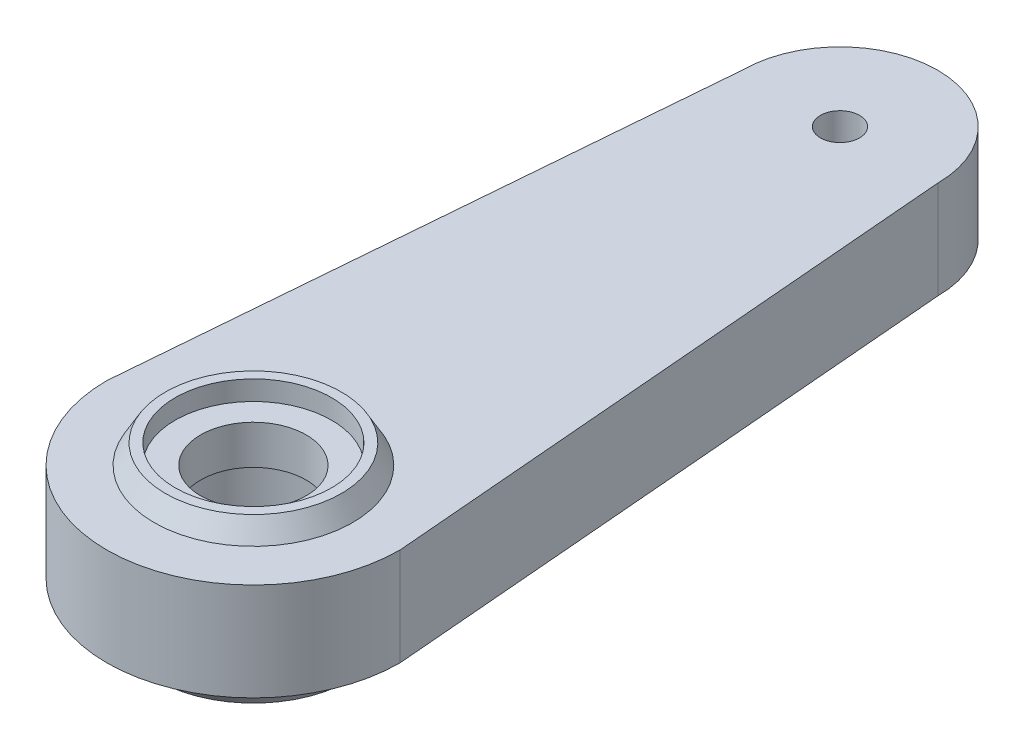
SolidWorks part; units mm, degrees
ref_plane "Front Plane" through (0, 0, 0) normal (0, 0, 1) x (1, 0, 0)
ref_plane "Top Plane" through (0, 0, 0) normal (0, 1, 0) x (1, 0, 0)
ref_plane "Right Plane" through (0, 0, 0) normal (1, 0, 0) x (0, 0, -1)
sketch "Sketch1" plane through (0, 0, 0) normal (0, 1, 0) x (1, 0, 0)
  line L1 (-7.5, 0) -> (-5, 30)
  line L2 (5, 30) -> (7.5, 0)
  arc A0 (-7.5, 0) -> (7.5, 0) centre (0, 0) ccw
  arc A2 (5, 30) -> (-5, 30) centre (0, 30) ccw
  dimension "D1" = 15
  dimension "D4" = 10
  dimension "D3" = 30
extrude "Boss-Extrude1" add sketch "Sketch1" along normal blind 5
sketch "Sketch2" plane through (0, 5, 0) normal (0, 1, 0) x (1, 0, 0)
  circle A0 centre (0, 0) radius 4
  circle A1 centre (0, 30) radius 1
  dimension "D1" = 8
  dimension "D2" = 2
extrude "Cut-Extrude1" cut sketch "Sketch2" against normal blind 5
sketch "Sketch3" plane through (0, 0, 0) normal (0, -1, 0) x (1, 0, 0)
  circle A0 centre (0, 0) radius 5
  circle A1 centre (0, 0) radius 4 construction
  dimension "D1" = 1
extrude "Boss-Extrude3" add sketch "Sketch3" along normal blind 2
draft "Draft3" type of draft neutral plane draft angle 30 faces to draft 1 face at (0, -2, -5) neutral plane through (0, -2, 0) neutral plane normal (0, -1, 0) parameters "D1"=30
sketch "Sketch4" plane through (0, 0, 0) normal (0, 1, 0) x (1, 0, 0)
  circle A1 centre (0, 0) radius 4
  circle A2 centre (0, 0) radius 4
  dimension "D1" = 0
extrude "Cut-Extrude2" cut sketch "Sketch4" against normal blind 2
sketch "Sketch5" plane through (0, 5, 0) normal (0, 1, 0) x (1, 0, 0)
  circle A0 centre (0, 0) radius 2.7009
  circle A1 centre (0, 0) radius 4
extrude "Boss-Extrude4" add sketch "Sketch5" against normal blind 2
sketch "Sketch6" plane through (0, 5, 0) normal (0, 1, 0) x (1, 0, 0)
  circle A0 centre (0, 0) radius 4
  circle A1 centre (0, 0) radius 4.5
  dimension "D1" = 8
  dimension "D2" = 9
extrude "Boss-Extrude5" add sketch "Sketch6" along normal blind 1
draft "Draft4" type of draft neutral plane draft angle 30 faces to draft 1 face at (0, 6, 4.5) neutral plane through (0, 6, 0) neutral plane normal (0, 1, 0) parameters "D1"=30
